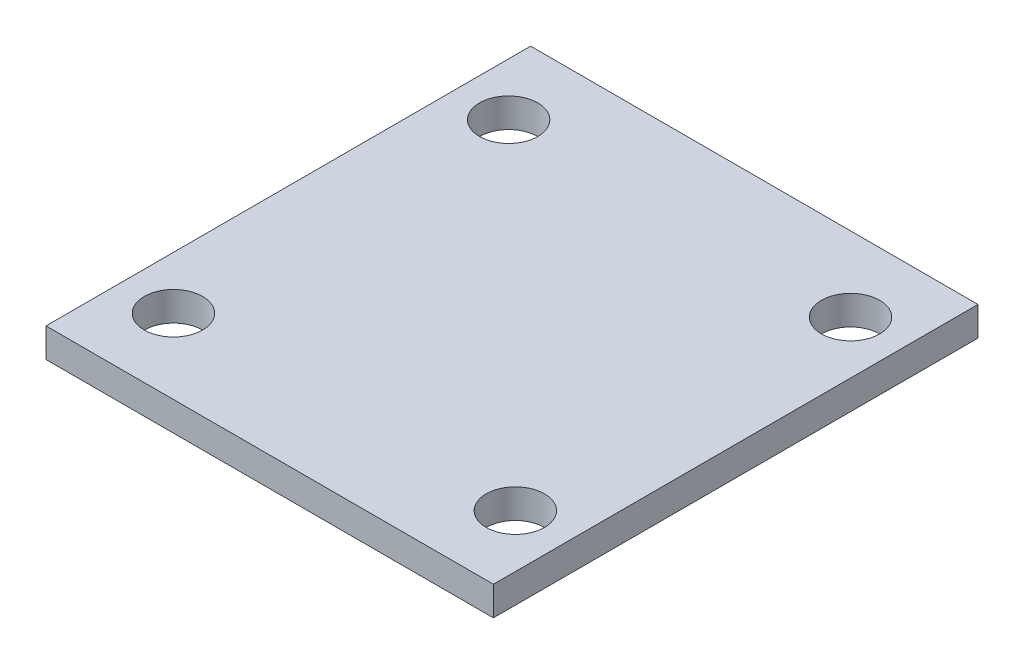
SolidWorks part; units mm, degrees
material "Custom Plastic"
ref_plane "Front Plane" through (0, 0, 0) normal (0, 0, 1) x (1, 0, 0)
ref_plane "Top Plane" through (0, 0, 0) normal (0, 1, 0) x (1, 0, 0)
ref_plane "Right Plane" through (0, 0, 0) normal (1, 0, 0) x (0, 0, -1)
sketch "Sketch1" plane through (0, 0, 0) normal (0, 1, 0) x (1, 0, 0)
  line L0 (0, 0) -> (0, 33.25)
  line L1 (0, 33.25) -> (30.7, 33.25)
  line L2 (30.7, 33.25) -> (30.7, 0)
  line L3 (30.7, 0) -> (0, 0)
  circle A0 centre (3.62, 28.125) radius 2
  circle A1 centre (27.08, 28.125) radius 2
  circle A2 centre (27.08, 5.125) radius 2
  circle A3 centre (3.62, 5.125) radius 2
  point P15 (26.901, 5.125)
  point P16 (26.901, 28.125)
  point P17 (3.8094, 5.125)
  point P21 (0, 0)
  point P24 (3.8094, 28.125)
extrude "Boss-Extrude1" add sketch "Sketch1" along normal blind 2
